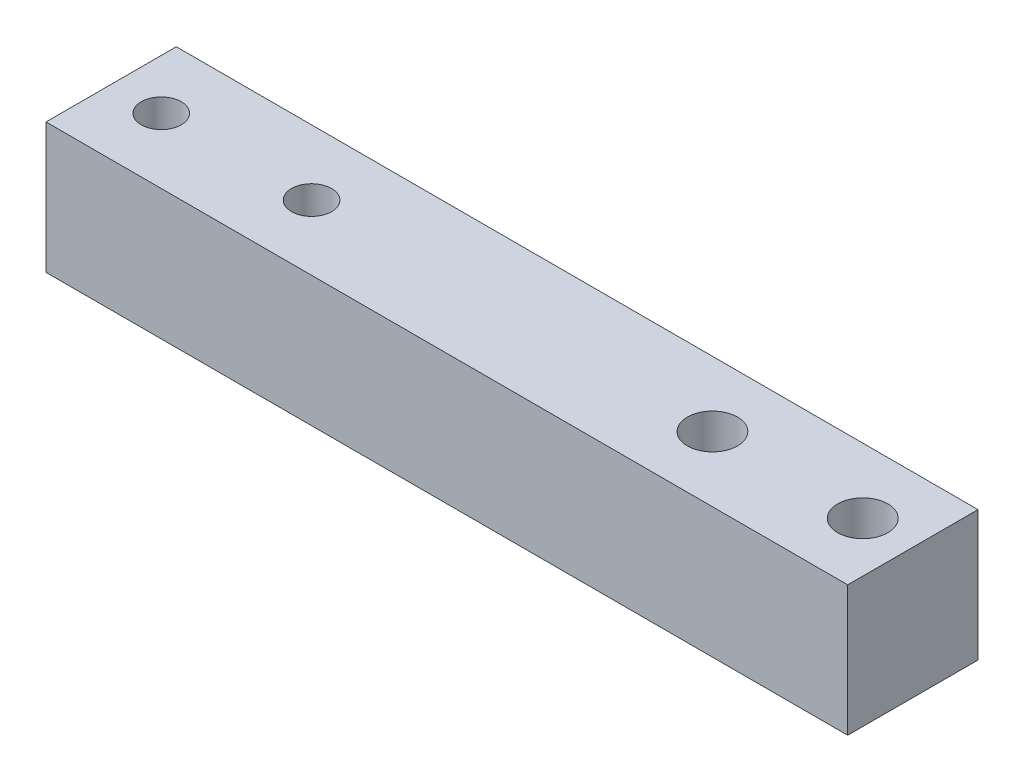
SolidWorks part; units mm, degrees
ref_plane "Plan de face" through (0, 0, 0) normal (0, 0, 1) x (1, 0, 0)
ref_plane "Plan de dessus" through (0, 0, 0) normal (0, 1, 0) x (1, 0, 0)
ref_plane "Plan de droite" through (0, 0, 0) normal (1, 0, 0) x (0, 0, -1)
sketch "Esquisse1" plane through (0, 0, 0) normal (0, 0, 1) x (1, 0, 0)
  line L1 (-2.5426, 1.5223) -> (77.4574, 1.5223)
  line L2 (-2.5426, 1.5223) -> (-2.5426, -11.4777)
  line L3 (-2.5426, -11.4777) -> (77.4574, -11.4777)
  line L4 (77.4574, 1.5223) -> (77.4574, -11.4777)
  dimension "D1" = 80
  dimension "D2" = 13
extrude "Boss.-Extru.1" add sketch "Esquisse1" along normal blind 13
sketch "Esquisse2" plane through (0, 1.5223, 0) normal (0, 1, 0) x (1, 0, 0)
  line L0 (37.4574, -13) -> (37.4574, 0) construction
  line L1 (37.4574, -6.5) -> (57.4574, -6.5) construction
  line L2 (57.4574, -6.5) -> (72.4574, -6.5) construction
  line L4 (77.4574, 0) -> (-2.5426, 0)
  line L5 (-2.5426, 0) -> (-2.5426, -13)
  line L6 (-2.5426, -13) -> (77.4574, -13)
  line L7 (77.4574, -13) -> (77.4574, 0)
  line L8 (77.4574, 0) -> (-2.5426, 0)
  line L9 (-2.5426, 0) -> (-2.5426, -13)
  line L10 (-2.5426, -13) -> (77.4574, -13)
  line L11 (77.4574, -13) -> (77.4574, 0)
  circle A0 centre (17.4574, -6.5) radius 2
  circle A1 centre (2.4574, -6.5) radius 2
  circle A2 centre (72.4574, -6.5) radius 2.5
  circle A3 centre (57.4574, -6.5) radius 2.5
  point P8 (2.4574, -6.5)
  point P10 (17.4574, -6.5)
  dimension "D4" = 5
  dimension "D5" = 5
  dimension "D6" = 4
  dimension "D7" = 4
  dimension "D2" = 20
  dimension "D3" = 15
  dimension "D1" = 0
extrude "Enlèv. mat.-Extru.1" cut sketch "Esquisse2" against normal through all contours A0 | A2 | A3 | A1
